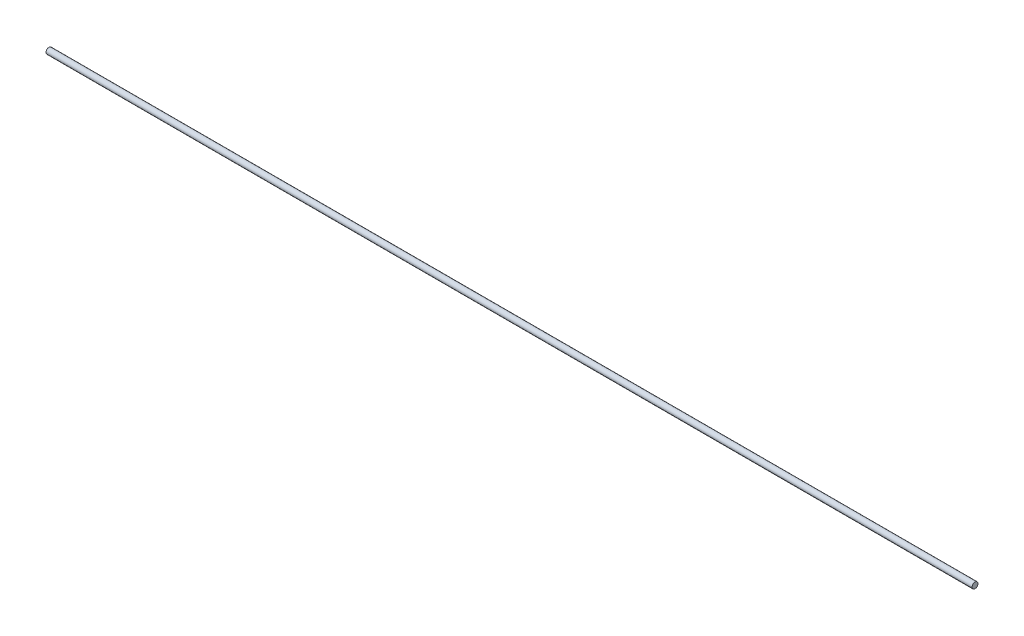
SolidWorks part; units mm, degrees
ref_plane "Front Plane" through (0, 0, 0) normal (0, 0, 1) x (1, 0, 0)
ref_plane "Top Plane" through (0, 0, 0) normal (0, 1, 0) x (1, 0, 0)
ref_plane "Right Plane" through (0, 0, 0) normal (1, 0, 0) x (0, 0, -1)
sketch "Sketch1" plane through (0, 0, 0) normal (1, 0, 0) x (0, 0, -1)
  circle A0 centre (0, 0) radius 0.003
  circle A1 centre (0, 0) radius 3
extrude "Boss-Extrude1" add sketch "Sketch1" along normal mid plane 938
